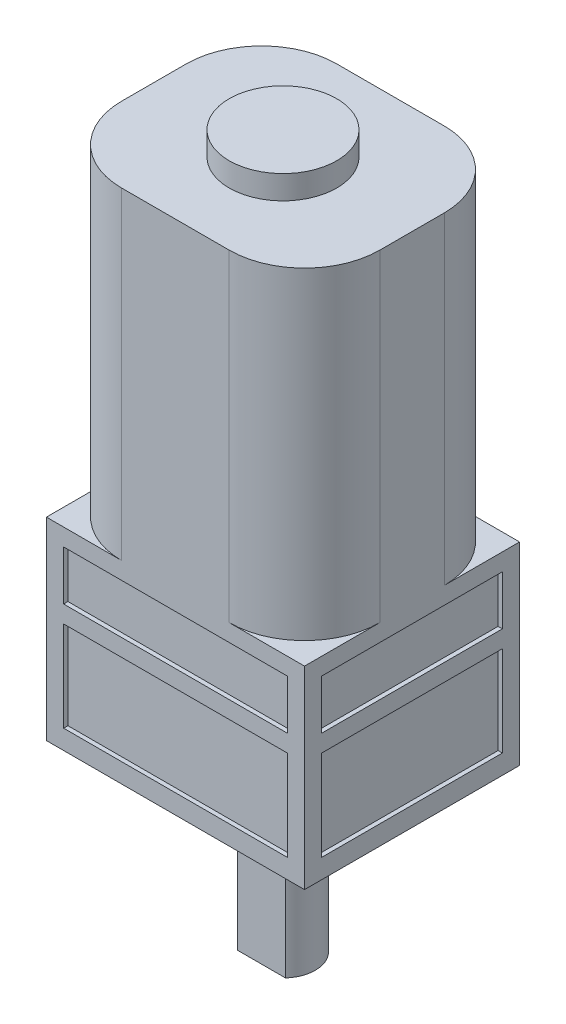
SolidWorks part; units mm, degrees
ref_plane "Front Plane" through (0, 0, 0) normal (0, 0, 1) x (1, 0, 0)
ref_plane "Top Plane" through (0, 0, 0) normal (0, 1, 0) x (1, 0, 0)
ref_plane "Right Plane" through (0, 0, 0) normal (1, 0, 0) x (0, 0, -1)
sketch "Sketch1" plane through (0, 0, 0) normal (0, 1, 0) x (1, 0, 0)
  line L0 (0, 0) -> (12.767, 0) construction
  line L1 (-6, 5) -> (6, 5)
  line L2 (-6, 5) -> (-6, -5)
  line L3 (-6, -5) -> (6, -5)
  line L4 (6, 5) -> (6, -5)
  line L5 (0, 0) -> (0, 11.6748) construction
  dimension "D1" = 12
  dimension "D2" = 10
extrude "Boss-Extrude1" add sketch "Sketch1" along normal blind 9
sketch "Sketch2" plane through (0, 9, 0) normal (0, 1, 0) x (1, 0, 0)
  line L0 (-6, -5) -> (6, -5) construction
  line L1 (-2.5, 5) -> (2.5, 5)
  line L2 (-6, 1.5) -> (-6, -1.5)
  line L3 (-2.5, -5) -> (2.5, -5)
  line L4 (6, 1.5) -> (6, -1.5)
  line L5 (-6, 5) -> (-6, -5) construction
  line L6 (6, 5) -> (-6, 5) construction
  line L7 (6, -5) -> (6, 5) construction
  arc A0 (-6, -1.5) -> (-2.5, -5) centre (-2.5, -1.5) ccw
  arc A1 (2.5, -5) -> (6, -1.5) centre (2.5, -1.5) ccw
  arc A2 (6, 1.5) -> (2.5, 5) centre (2.5, 1.5) ccw
  arc A3 (-6, 1.5) -> (-2.5, 5) centre (-2.5, 1.5) cw
  dimension "D1" = 3.5
extrude "Boss-Extrude2" add sketch "Sketch2" along normal blind 15
sketch "Sketch3" plane through (0, 24, 0) normal (0, 1, 0) x (1, 0, 0)
  circle A0 centre (0, 0) radius 2.5
  dimension "D1" = 5
extrude "Boss-Extrude3" add sketch "Sketch3" along normal blind 1.1
sketch "Sketch4" plane through (0, 0, 0) normal (0, -1, 0) x (1, 0, 0)
  line L0 (-1.118, 1) -> (1.118, 1)
  arc A0 (-1.118, 1) -> (1.118, 1) centre (0, 0) ccw
  dimension "D1" = 3
  dimension "D2" = 1
extrude "Boss-Extrude4" add sketch "Sketch4" along normal blind 8
sketch "Sketch5" plane through (0, 0, 5) normal (0, 0, 1) x (1, 0, 0)
  line L0 (6, 9) -> (2.5, 9) construction
  line L1 (-5.2, 8.2) -> (5.2, 8.2)
  line L2 (-5.2, 8.2) -> (-5.2, 5.9)
  line L3 (-5.2, 5.9) -> (5.2, 5.9)
  line L4 (5.2, 8.2) -> (5.2, 5.9)
  line L5 (-5.2, 5.1) -> (5.2, 5.1)
  line L6 (-5.2, 5.1) -> (-5.2, 0.9)
  line L7 (-5.2, 0.9) -> (5.2, 0.9)
  line L8 (5.2, 5.1) -> (5.2, 0.9)
  line L9 (-6, 9) -> (-6, 0) construction
  line L10 (6, 9) -> (6, 0) construction
  dimension "D1" = 0.8
  dimension "D2" = 2.3
  dimension "D3" = 0.8
  dimension "D4" = 4.2
  dimension "D5" = 0.8
  dimension "D6" = 0.8
extrude "Cut-Extrude1" cut sketch "Sketch5" against normal blind 0.2
mirror "Mirror1" about plane through (0, 0, 0) normal (0, 0, 1) of "Cut-Extrude1"
sketch "Sketch6" plane through (-6, 0, 0) normal (-1, 0, 0) x (0, 0, 1)
  line L0 (5, 9) -> (5, 0) construction
  line L1 (-4.2, 8.2) -> (4.2, 8.2)
  line L2 (-4.2, 8.2) -> (-4.2, 5.9)
  line L3 (-4.2, 5.9) -> (4.2, 5.9)
  line L4 (4.2, 8.2) -> (4.2, 5.9)
  line L5 (-5, 9) -> (-5, 0) construction
  line L7 (-4.2, 5.1) -> (4.2, 5.1)
  line L8 (-4.2, 5.1) -> (-4.2, 0.9)
  line L9 (-4.2, 0.9) -> (4.2, 0.9)
  line L10 (4.2, 5.1) -> (4.2, 0.9)
  point P15 (0, 0)
  dimension "D1" = 0.8
  dimension "D3" = 0.8
extrude "Cut-Extrude2" cut sketch "Sketch6" against normal blind 0.2
mirror "Mirror2" about plane through (0, 0, 0) normal (1, 0, 0) of "Cut-Extrude2"
